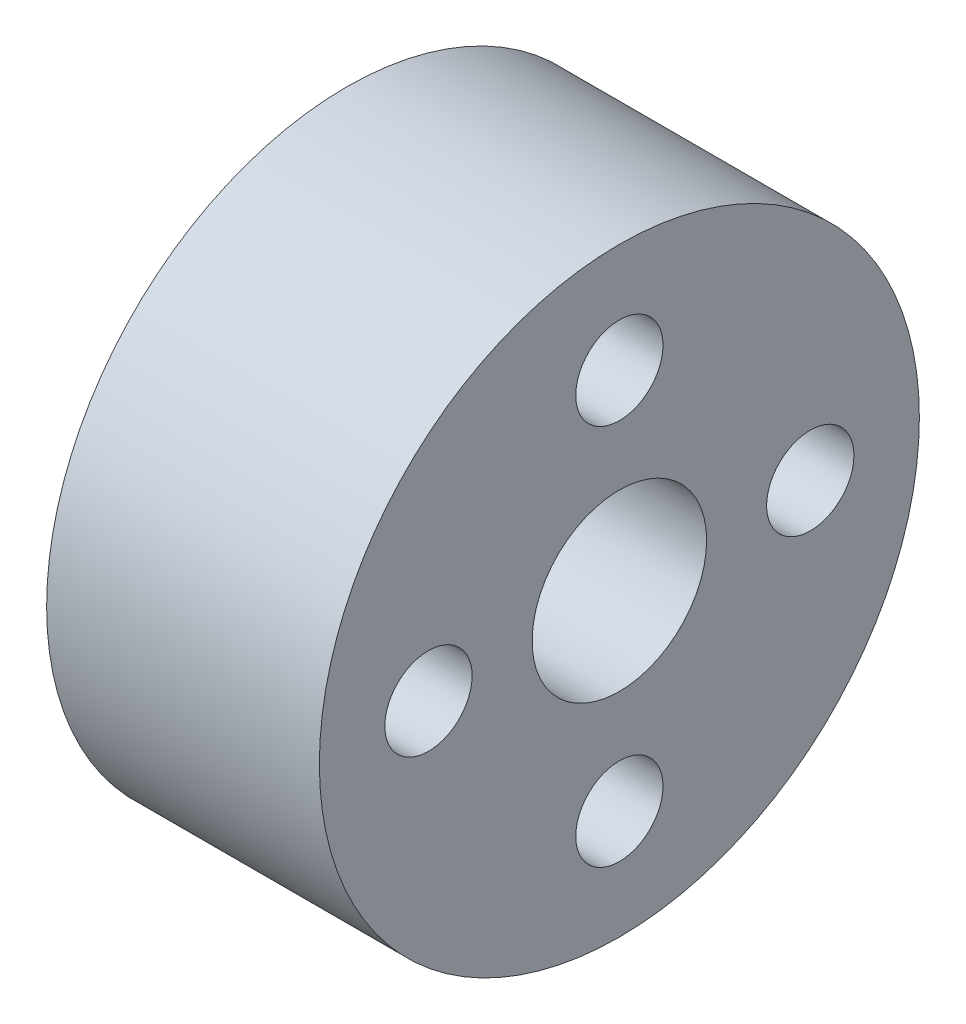
SolidWorks part; units mm, degrees
material "Carbon Sandwich"
ref_plane "Front Plane" through (0, 0, 0) normal (0, 0, 1) x (1, 0, 0)
ref_plane "Top Plane" through (0, 0, 0) normal (0, 1, 0) x (1, 0, 0)
ref_plane "Right Plane" through (0, 0, 0) normal (1, 0, 0) x (0, 0, -1)
sketch "Sketch1" plane through (0, 0, 0) normal (1, 0, 0) x (0, 0, -1)
  circle A1 centre (0, 0) radius 7 construction
  circle A2 centre (0, 7) radius 1.6
  circle A3 centre (-7, 0) radius 1.6
  circle A4 centre (0, -7) radius 1.6
  circle A5 centre (7, 0) radius 1.6
  circle A6 centre (0, 0) radius 11
  circle A7 centre (0, 0) radius 3.2
  dimension "D1" = 3.2
  dimension "D2" = 14
  dimension "D3" = 22
  dimension "D4" = 6.4
extrude "Boss-Extrude1" add sketch "Sketch1" along normal blind 10
